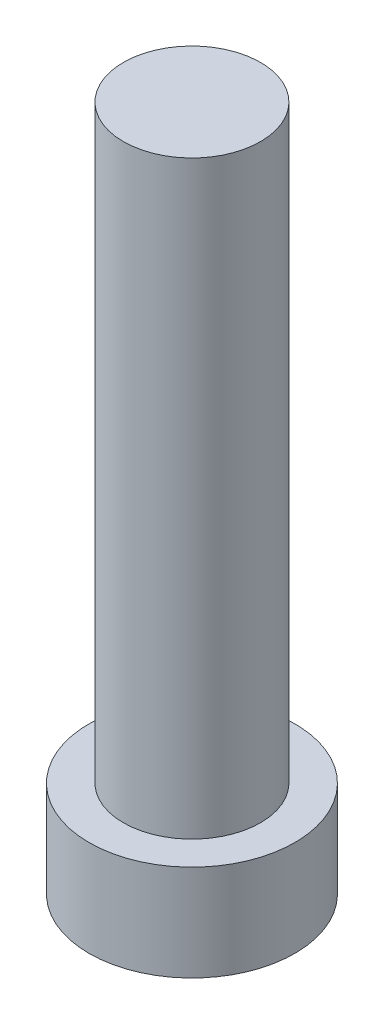
SolidWorks part; units mm, degrees
ref_plane "Front Plane" through (0, 0, 0) normal (0, 0, 1) x (1, 0, 0)
ref_plane "Top Plane" through (0, 0, 0) normal (0, 1, 0) x (1, 0, 0)
ref_plane "Right Plane" through (0, 0, 0) normal (1, 0, 0) x (0, 0, -1)
sketch "Sketch1" plane through (0, 0, 0) normal (0, 1, 0) x (1, 0, 0)
  circle A0 centre (0, 0) radius 7.5
  dimension "D1" = 15
extrude "Boss-Extrude1" add sketch "Sketch1" along normal blind 7
sketch "Sketch2" plane through (0, 7, 0) normal (0, 1, 0) x (1, 0, 0)
  circle A0 centre (0, 0) radius 5
  dimension "D1" = 10
extrude "Boss-Extrude2" add sketch "Sketch2" along normal blind 43
